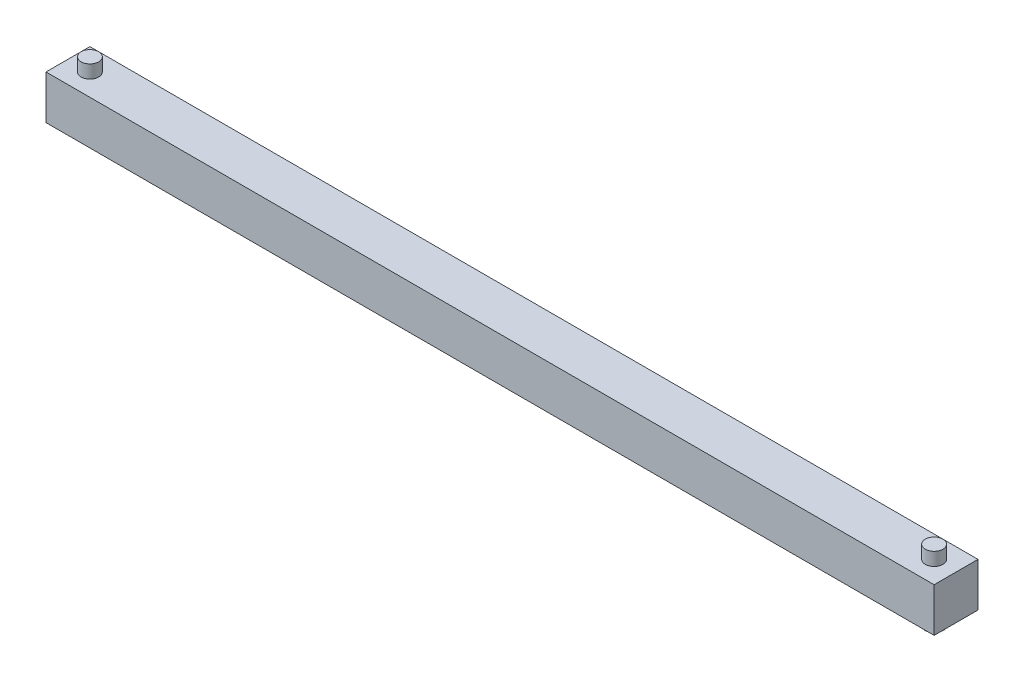
SolidWorks part; units mm, degrees
ref_plane "前视基准面" through (0, 0, 0) normal (0, 0, 1) x (1, 0, 0)
ref_plane "上视基准面" through (0, 0, 0) normal (0, 1, 0) x (1, 0, 0)
ref_plane "右视基准面" through (0, 0, 0) normal (1, 0, 0) x (0, 0, -1)
sketch "草图1" plane through (0, 0, 0) normal (0, 0, 1) x (1, 0, 0)
  line L0 (-92.583, -5.3136) -> (-96.583, -5.3136)
  line L1 (-92.583, -5.3136) -> (61.2687, -5.3136)
  line L2 (-92.583, -5.3136) -> (-92.583, -13.3136)
  line L3 (-92.583, -13.3136) -> (61.2687, -13.3136)
  line L4 (61.2687, -5.3136) -> (61.2687, -13.3136)
  line L5 (-96.583, -5.3136) -> (-96.583, -13.3136)
  line L6 (-96.583, -13.3136) -> (-92.583, -13.3136)
  line L7 (61.2687, -5.3136) -> (65.2687, -5.3136)
  line L8 (61.2687, -13.3136) -> (65.2687, -13.3136)
  line L9 (65.2687, -13.3136) -> (65.2687, -5.3136)
extrude "凸台-拉伸1" add sketch "草图1" along normal blind 8 contours L5 L6 L2 L0 | L4 L1 L2 L3 | L8 L9 L7 L4
sketch "草图2" plane through (0, -5.3136, 0) normal (0, 1, 0) x (1, 0, 0)
  line L0 (-96.583, -4) -> (-92.583, -4)
  line L1 (-96.583, -8) -> (-96.583, 0) construction
  line L2 (65.2687, -8) -> (65.2687, 0) construction
  line L3 (65.2687, -4) -> (61.2687, -4)
  circle A0 centre (-92.583, -4) radius 1.6
  circle A1 centre (61.2687, -4) radius 1.6
extrude "凸台-拉伸2" add sketch "草图2" along normal blind 2.4
sketch "草图3" plane through (0, -13.3136, 0) normal (0, -1, 0) x (-1, 0, 0)
  line L0 (96.583, -4) -> (92.583, -4)
  line L1 (96.583, -8) -> (96.583, 0) construction
  line L2 (-65.2687, -4) -> (-61.2687, -4)
  line L3 (-65.2687, -8) -> (-65.2687, 0) construction
  circle A0 centre (92.583, -4) radius 1.6
  circle A1 centre (-61.2687, -4) radius 1.65
extrude "凸台-拉伸3" add sketch "草图3" along normal blind 2.4
